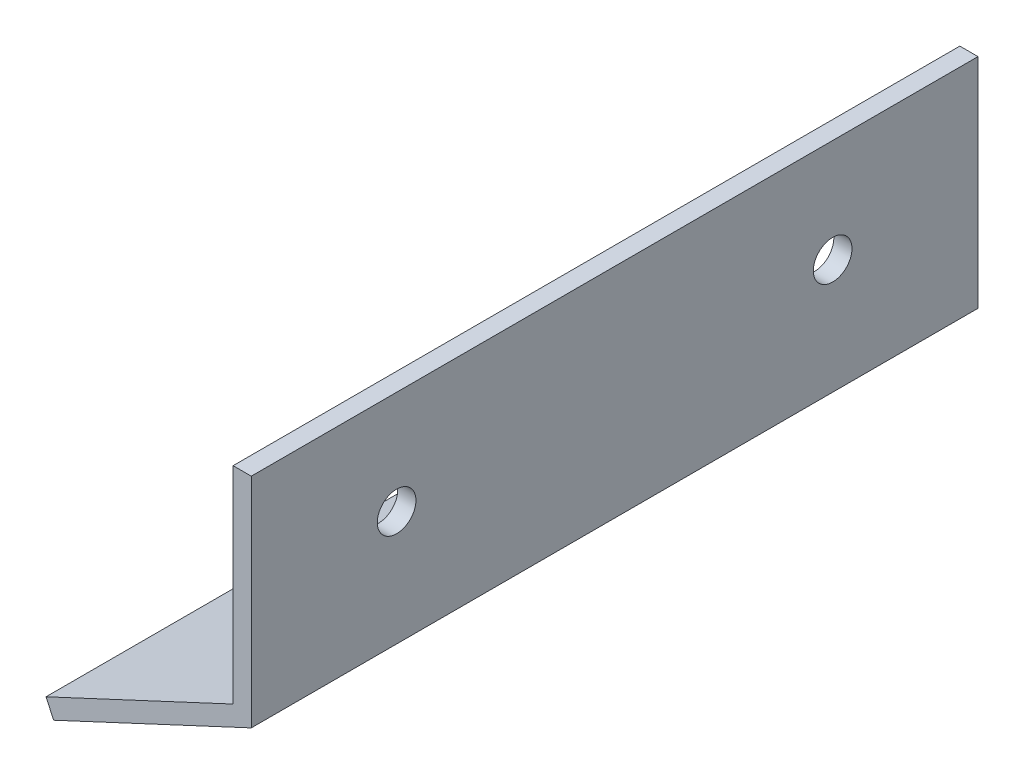
SolidWorks part; units mm, degrees
material "6061 Alloy"
ref_plane "Front Plane" through (0, 0, 0) normal (0, 0, 1) x (1, 0, 0)
ref_plane "Top Plane" through (0, 0, 0) normal (0, 1, 0) x (1, 0, 0)
ref_plane "Right Plane" through (0, 0, 0) normal (1, 0, 0) x (0, 0, -1)
sketch "Sketch1" plane through (0, 0, 0) normal (0, 0, 1) x (1, 0, 0)
  line L0 (0, 0) -> (0, 38.1)
  line L1 (0, 0) -> (-34.5303, -16.1018)
  line L2 (-3.175, 2.0227) -> (-35.8721, -13.2242)
  line L3 (-3.175, 2.0227) -> (-3.175, 38.1)
  line L4 (-35.8721, -13.2242) -> (-34.5303, -16.1018)
  line L5 (-3.175, 38.1) -> (0, 38.1)
  dimension "D1" = 38.1
  dimension "D2" = 115
  dimension "D3" = 38.1
  dimension "D4" = 3.175
extrude "Boss-Extrude1" add sketch "Sketch1" along normal mid plane 127
sketch "Sketch2" plane through (-3.175, 0, 0) normal (-1, 0, 0) x (0, 0, 1)
  line L0 (-63.5, 20.0613) -> (63.5, 20.0613) construction
  line L1 (-63.5, 38.1) -> (-63.5, 2.0227) construction
  line L2 (63.5, 38.1) -> (63.5, 2.0227) construction
  point P6 (-38.1, 20.0613)
  point P7 (38.1, 20.0613)
  dimension "D1" = 25.4
  dimension "D2" = 25.4
sketch "Sketch3" plane through (-1.3418, 2.8775, 0) normal (-0.4226, 0.9063, 0) x (0.9063, 0.4226, 0)
  line L0 (-20.0613, 63.5) -> (-20.0613, -63.5) construction
  line L1 (-2.0227, 63.5) -> (-38.1, 63.5) construction
  line L2 (-2.0227, -63.5) -> (-38.1, -63.5) construction
  point P6 (-20.0613, 38.1)
  point P7 (-20.0613, -38.1)
  dimension "D1" = 25.4
  dimension "D2" = 25.4
hole_wizard "1/4 Clearance Hole1" positions "3DSketch1" profile "Sketch5" hole size "1/4" standard "ANSI Inch" end condition through all
sketch3d "3DSketch1"
  point P0 (-3.175, 20.0613, -38.1)
  point P3 (-3.175, 20.0613, 38.1)
  point P6 (-19.5236, -5.6008, -38.1)
  point P9 (-19.5236, -5.6008, 38.1)
sketch "Sketch5" plane through (-3.175, 20.0613, -38.1) normal (0, 1, 0) x (0, 0, 1)
  line L0 (0, 0) -> (0, 3.175)
  line L1 (0, 3.175) -> (3.3782, 3.175)
  line L2 (3.3782, 3.175) -> (3.3782, 0)
  line L5 (3.3782, 0) -> (0, 0)
  line L11 (0, -6.35) -> (0, 107.95) construction
  dimension "Thru Hole Dia." = 6.7564
  dimension "Thru Hole Depth" = 3.175
